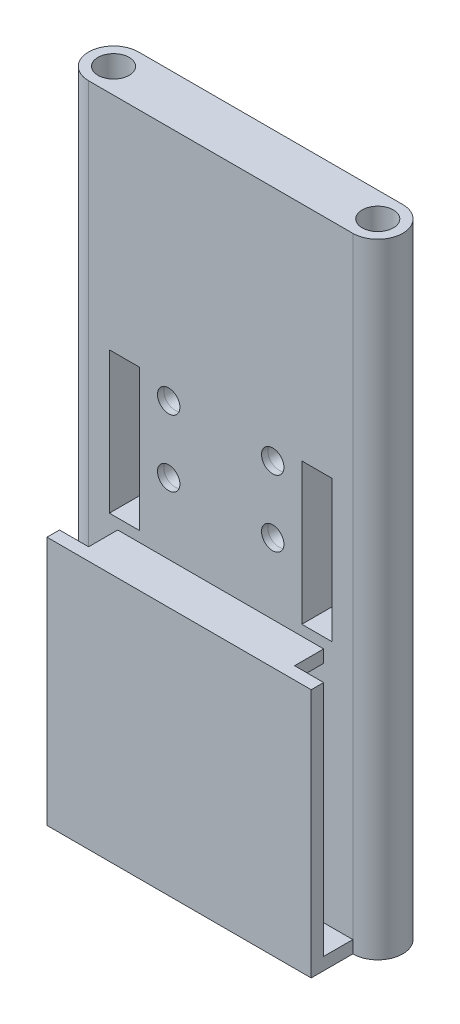
SolidWorks part; units mm, degrees
ref_plane "Front Plane" through (0, 0, 0) normal (0, 0, 1) x (1, 0, 0)
ref_plane "Top Plane" through (0, 0, 0) normal (0, 1, 0) x (1, 0, 0)
ref_plane "Right Plane" through (0, 0, 0) normal (1, 0, 0) x (0, 0, -1)
ref_plane "Plane1" through (12.7, 0, 0) normal (1, 0, 0) x (0, 0, -1)
sketch "Sketch1" plane through (0, 0, 0) normal (0, 1, 0) x (1, 0, 0)
  line L0 (-31.75, -6) -> (0, -6)
  line L1 (0, -6) -> (0, 6)
  line L2 (0, 6) -> (-31.75, 6)
  circle A0 centre (-31.75, 0) radius 3.75
  arc A3 (-31.75, -6) -> (-31.75, 6) centre (-31.75, 0) cw
  dimension "D1" = 7.5
  dimension "D3" = 31.75
extrude "Boss-Extrude1" add sketch "Sketch1" along normal blind 150 contours A3 L0 L1 L2 A0
mirror "Mirror1" about plane through (0, 150, 0) normal (-1, 0, 0) of "Boss-Extrude1"
sketch "Sketch2" plane through (12.7, 0, -12.7) normal (-1, 0, 0) x (0, 0, 1)
  line L0 (6.2, 65) -> (15.5998, 65)
  line L1 (15.5998, 65) -> (15.5998, 62.75)
  line L2 (15.5998, 62.75) -> (11.5999, 62.7717)
  line L3 (11.5999, 62.7717) -> (8.1999, 62.3217)
  line L4 (8.1999, 62.3217) -> (6.2, 62.3)
  line L5 (6.2, 62.3) -> (6.2, 65)
  line L6 (6.7, 150) -> (6.7, 0) construction
  dimension "D1" = 2
  dimension "D2" = 2.7
  dimension "D3" = 2.25
  dimension "D4" = 4
  dimension "D5" = 3.4
  dimension "D6" = 0.45
  dimension "D7" = 0.5
  dimension "D8" = 65
  dimension "D9" = 187.851
  dimension "D10" = 89.689
  dimension "D11" = 173.083
revolve "Cut-Revolve1" cut sketch "Sketch2" angle 360 about L0
pattern_linear "LPattern1" count 2 spacing 76.2 along (0, 1, 0) count 2 spacing 25.4 along (-1, 0, 0) of "Cut-Revolve1"
ref_plane "Plane2" through (15.75, 0, 0) normal (1, 0, 0) x (0, 0, -1)
sketch "Sketch3" plane through (15.75, 0, 3.05) normal (-1, 0, 0) x (0, 0, 1)
  line L0 (-9.55, 20) -> (-0.1502, 20)
  line L1 (-0.1502, 20) -> (-0.1502, 17.75)
  line L2 (-0.1502, 17.75) -> (-4.1501, 17.7717)
  line L3 (-4.1501, 17.7717) -> (-7.5501, 17.3217)
  line L4 (-7.5501, 17.3217) -> (-9.55, 17.3)
  line L5 (-9.55, 17.3) -> (-9.55, 20)
  line L6 (-9.05, 150) -> (-9.05, 0) construction
  dimension "D1" = 2
  dimension "D2" = 2.7
  dimension "D3" = 2.25
  dimension "D4" = 4
  dimension "D5" = 3.4
  dimension "D6" = 0.45
  dimension "D7" = 0.5
  dimension "D8" = 20
  dimension "D9" = 187.851
  dimension "D10" = 89.689
  dimension "D11" = 173.083
revolve "Cut-Revolve2" cut sketch "Sketch3" angle 360 about L0
pattern_linear "LPattern2" count 2 spacing 14 along (0, 1, 0) count 2 spacing 31.5 along (-1, 0, 0) of "Cut-Revolve2"
ref_plane "Plane3" through (12.5, 0, 0) normal (1, 0, 0) x (0, 0, -1)
sketch "Sketch4" plane through (12.5, 0, 15.55) normal (-1, 0, 0) x (0, 0, 1)
  line L0 (-9.05, 77) -> (-18.4498, 77)
  line L1 (-18.4498, 77) -> (-18.4498, 79.25)
  line L2 (-18.4498, 79.25) -> (-14.4499, 79.2283)
  line L3 (-14.4499, 79.2283) -> (-11.0499, 79.6783)
  line L4 (-11.0499, 79.6783) -> (-9.05, 79.7)
  line L5 (-9.05, 79.7) -> (-9.05, 77)
  line L6 (-9.55, 150) -> (-9.55, 0) construction
  dimension "D1" = 2
  dimension "D2" = 2.7
  dimension "D3" = 2.25
  dimension "D4" = 4
  dimension "D5" = 3.4
  dimension "D6" = 0.45
  dimension "D7" = 90
  dimension "D8" = 0.5
  dimension "D9" = 187.851
  dimension "D10" = 89.689
  dimension "D11" = 173.083
  dimension "D12" = 77
revolve "Cut-Revolve3" cut sketch "Sketch4" angle 360 about L0
pattern_linear "LPattern3" count 2 spacing 16 along (0, 1, 0) count 2 spacing 25 along (-1, 0, 0) of "Cut-Revolve3"
sketch "Sketch6" plane through (0, 0, 6) normal (0, 0, 1) x (1, 0, 0)
  line L0 (31.75, 150) -> (31.75, 0) construction
  line L1 (-31.75, 0) -> (31.75, 0)
  line L2 (-31.75, 0) -> (-31.75, 60)
  line L3 (-31.75, 60) -> (31.75, 60)
  line L4 (31.75, 0) -> (31.75, 60)
  dimension "D1" = 60
extrude "Boss-Extrude2" add sketch "Sketch6" along normal blind 10
sketch "Sketch7" plane through (0, 0, 6) normal (0, 0, 1) x (1, 0, 0)
  line L0 (-31.75, 60) -> (-31.75, 0) construction
  line L1 (-2, 3) -> (-31.75, 3)
  line L2 (-2, 3) -> (-2, 57)
  line L3 (-2, 57) -> (-24.75, 57)
  line L4 (-31.75, 3) -> (-31.75, 57)
  line L5 (-31.75, 0) -> (31.75, 0) construction
  line L6 (31.75, 60) -> (-31.75, 60) construction
  line L7 (31.75, 60) -> (-31.75, 60) construction
  line L9 (-31.75, 57) -> (-31.75, 60)
  line L10 (-31.75, 60) -> (-24.75, 60)
  line L11 (-24.75, 57) -> (-24.75, 60)
  dimension "D1" = 2
  dimension "D2" = 3
  dimension "D3" = 3
  dimension "D4" = 7
extrude "Cut-Extrude1" cut sketch "Sketch7" along normal offset from surface (7 mm away) 3 up to face at (0, 30, 16)
mirror "Mirror2" about plane through (0, 0, 0) normal (1, 0, 0) of "Cut-Extrude1"
sketch "Sketch8" plane through (0, 0, 6) normal (0, 0, 1) x (1, 0, 0)
  line L0 (-31.75, 150) -> (-31.75, 3) construction
  line L1 (-19.5, 62.5) -> (-26.75, 62.5)
  line L2 (-19.5, 62.5) -> (-19.5, 96.5)
  line L3 (-19.5, 96.5) -> (-26.75, 96.5)
  line L4 (-26.75, 62.5) -> (-26.75, 96.5)
  circle A0 centre (-12.5, 77) radius 2.6946 construction
  circle A1 centre (-12.5, 93) radius 2.6946 construction
  dimension "D4" = 3.5
  dimension "D1" = 7
  dimension "D2" = 5
  dimension "D3" = 34
extrude "Cut-Extrude2" cut sketch "Sketch8" against normal through all
mirror "Mirror3" about plane through (0, 0, 0) normal (1, 0, 0) of "Cut-Extrude2"
